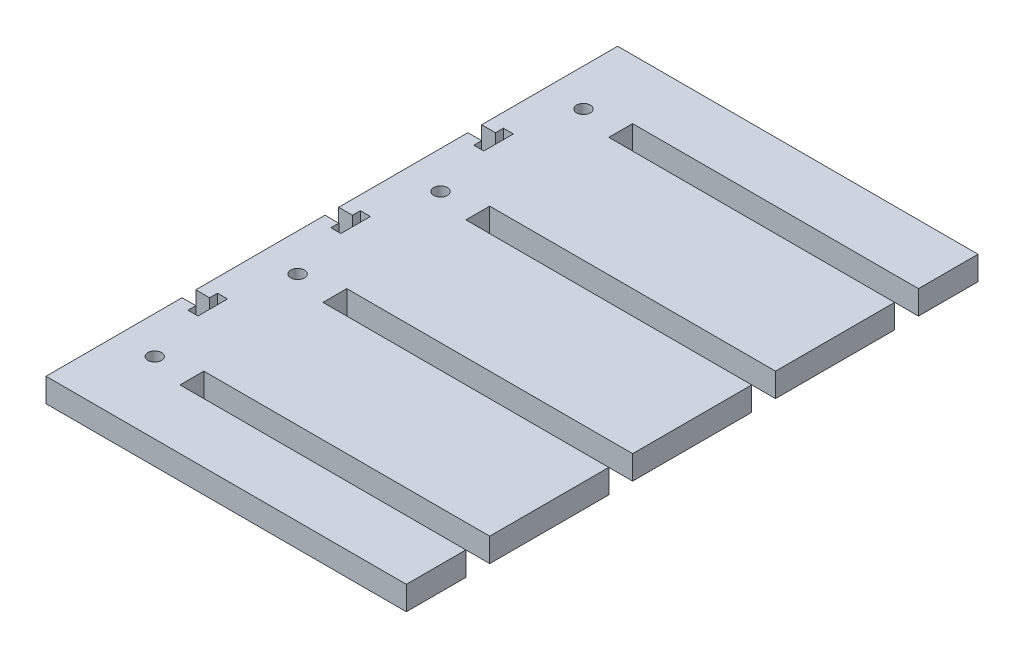
SolidWorks part; units mm, degrees
ref_plane "Front Plane" through (0, 0, 0) normal (0, 0, 1) x (1, 0, 0)
ref_plane "Top Plane" through (0, 0, 0) normal (0, 1, 0) x (1, 0, 0)
ref_plane "Right Plane" through (0, 0, 0) normal (1, 0, 0) x (0, 0, -1)
sketch "Sketch1" plane through (0, 0, 0) normal (0, 1, 0) x (1, 0, 0)
  line L0 (-38.1, 57.15) -> (-38.1, -76.2) construction
  line L1 (-48.0314, 76.2) -> (48.0314, 76.2)
  line L2 (-48.0314, 76.2) -> (-48.0314, 39.9288)
  line L3 (-48.0314, -76.2) -> (48.0314, -76.2)
  line L4 (48.0314, 76.2) -> (48.0314, 60.325)
  line L5 (-48.0314, 76.2) -> (48.0314, -76.2) construction
  line L6 (-48.0314, -76.2) -> (48.0314, 76.2) construction
  line L7 (-38.1, 57.15) -> (48.0314, 57.15) construction
  line L8 (48.0314, 60.325) -> (-28.1686, 60.325)
  line L9 (48.0314, 53.975) -> (-28.1686, 53.975)
  line L10 (-28.1686, 60.325) -> (-28.1686, 53.975)
  line L11 (48.0314, 53.975) -> (48.0314, 22.225)
  line L12 (48.0314, 15.875) -> (-28.1686, 15.875)
  line L13 (-28.1686, 22.225) -> (-28.1686, 15.875)
  line L14 (48.0314, 22.225) -> (-28.1686, 22.225)
  line L15 (48.0314, -22.225) -> (-28.1686, -22.225)
  line L16 (-28.1686, -15.875) -> (-28.1686, -22.225)
  line L17 (48.0314, -15.875) -> (-28.1686, -15.875)
  line L18 (48.0314, -60.325) -> (-28.1686, -60.325)
  line L19 (-28.1686, -53.975) -> (-28.1686, -60.325)
  line L20 (48.0314, -53.975) -> (-28.1686, -53.975)
  line L21 (48.0314, 15.875) -> (48.0314, -15.875)
  line L22 (48.0314, -22.225) -> (48.0314, -53.975)
  line L23 (48.0314, -60.325) -> (48.0314, -76.2)
  line L24 (-38.1, 57.15) -> (-38.1, 19.05) construction
  line L25 (-38.1, 38.1) -> (-48.0314, 38.1) construction
  line L26 (-48.0314, 39.9288) -> (-44.3484, 39.9288)
  line L27 (-44.3484, 39.9288) -> (-44.3484, 42.037)
  line L28 (-44.3484, 42.037) -> (-41.6814, 42.037)
  line L29 (-41.6814, 42.037) -> (-41.6814, 34.163)
  line L30 (-44.3484, 34.163) -> (-41.6814, 34.163)
  line L31 (-44.3484, 36.2712) -> (-44.3484, 34.163)
  line L32 (-48.0314, 36.2712) -> (-44.3484, 36.2712)
  line L33 (-48.0314, 1.8288) -> (-44.3484, 1.8288)
  line L34 (-48.0314, -1.8288) -> (-44.3484, -1.8288)
  line L35 (-44.3484, -1.8288) -> (-44.3484, -3.937)
  line L36 (-44.3484, -3.937) -> (-41.6814, -3.937)
  line L37 (-41.6814, 3.937) -> (-41.6814, -3.937)
  line L38 (-44.3484, 3.937) -> (-41.6814, 3.937)
  line L39 (-44.3484, 1.8288) -> (-44.3484, 3.937)
  line L40 (-48.0314, -36.2712) -> (-44.3484, -36.2712)
  line L41 (-48.0314, -39.9288) -> (-44.3484, -39.9288)
  line L42 (-44.3484, -39.9288) -> (-44.3484, -42.037)
  line L43 (-44.3484, -42.037) -> (-41.6814, -42.037)
  line L44 (-41.6814, -34.163) -> (-41.6814, -42.037)
  line L45 (-44.3484, -34.163) -> (-41.6814, -34.163)
  line L46 (-44.3484, -36.2712) -> (-44.3484, -34.163)
  line L47 (-48.0314, 36.2712) -> (-48.0314, 1.8288)
  line L48 (-48.0314, -1.8288) -> (-48.0314, -36.2712)
  line L49 (-48.0314, -39.9288) -> (-48.0314, -76.2)
  circle A0 centre (-38.1, 57.15) radius 1.8288
  circle A1 centre (-38.1, 19.05) radius 1.8288
  circle A2 centre (-38.1, -19.05) radius 1.8288
  circle A3 centre (-38.1, -57.15) radius 1.8288
  point P0 (0, 0)
  point P40 (-41.6814, 38.1)
  dimension "D9" = 3.6576
  dimension "D1" = 152.4
  dimension "D2" = 96.0628
  dimension "D3" = 9.9314
  dimension "D4" = 19.05
  dimension "D6" = 3.175
  dimension "D7" = 76.2
  dimension "D10" = 3.6576
  dimension "D11" = 6.35
  dimension "D12" = 2.667
  dimension "D13" = 7.874
  dimension "D14" = 19.05
  dimension "D5" = 4
  dimension "D8" = 4
  dimension "D15" = 3
extrude "Boss-Extrude1" add sketch "Sketch1" against normal blind 6.35
